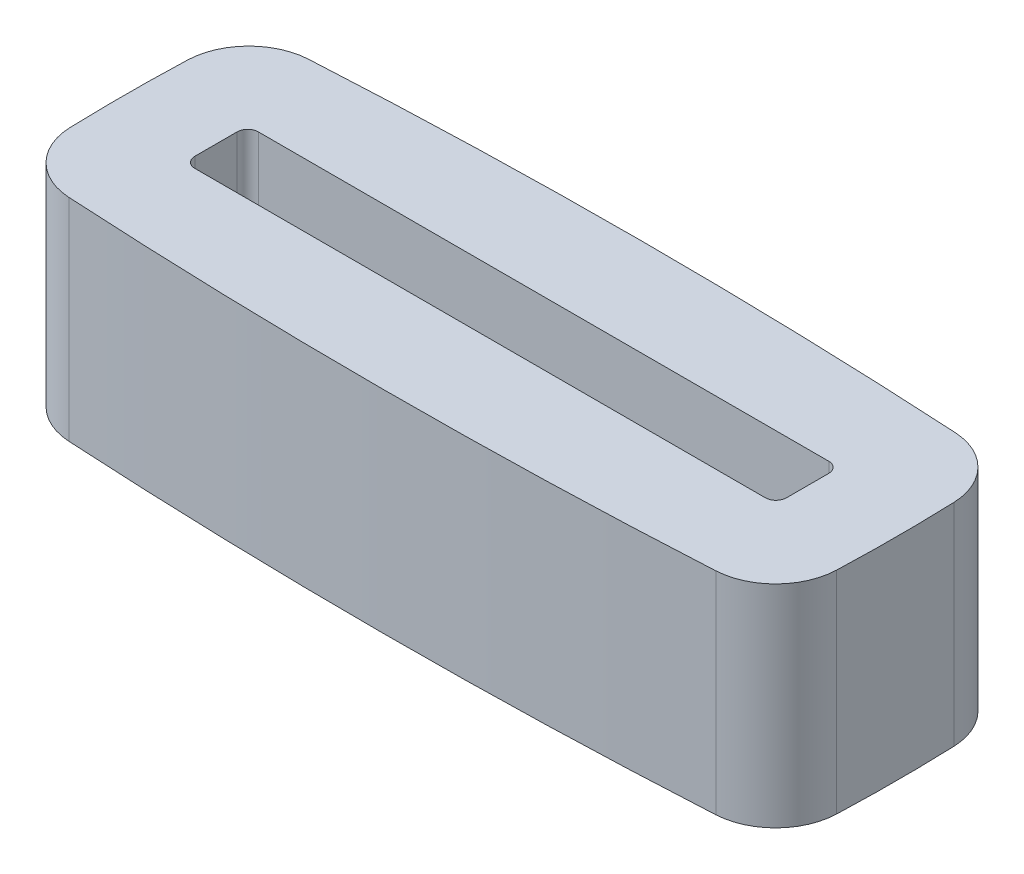
SolidWorks part; units mm, degrees
material "Медь"
ref_plane "Спереди" through (0, 0, 0) normal (0, 0, 1) x (1, 0, 0)
ref_plane "Сверху" through (0, 0, 0) normal (0, 1, 0) x (1, 0, 0)
ref_plane "Справа" through (0, 0, 0) normal (1, 0, 0) x (0, 0, -1)
sketch "Эскиз1" plane through (0, 0, 0) normal (0, 1, 0) x (1, 0, 0)
  line L7 (6.029, -0.585) -> (-21.971, -0.585)
  line L8 (6.029, -0.585) -> (6.029, 2.415)
  line L9 (6.029, 2.415) -> (-21.971, 2.415)
  line L10 (-21.971, -0.585) -> (-21.971, 2.415)
  arc A0 (-25.9419, 6.415) -> (10.029, 6.415) centre (-7.9565, -262.8497) cw
  arc A1 (-25.971, -4.585) -> (10.029, -4.585) centre (-7.971, 265.115) ccw
  arc A2 (-25.971, -4.585) -> (-25.9419, 6.415) centre (55.4935, 0.7001) cw
  arc A3 (10.029, 6.415) -> (10.029, -4.585) centre (-65.496, 0.915) cw
  point P1 (0, 0)
  point P6 (0, 0)
  point P15 (-7.9565, 7.015)
  point P16 (-7.971, -5.185)
  point P17 (-26.1419, 0.9155)
  point P18 (10.229, 0.915)
  dimension "D1" = 11
  dimension "D2" = 36
  dimension "D3" = 3
  dimension "D4" = 28
  dimension "D5" = 0.6
  dimension "D6" = 0.6
  dimension "D7" = 0.2
  dimension "D8" = 0.2
  dimension "D9" = 4
  dimension "D10" = 4
  dimension "D11" = 11
  dimension "D12" = 4
  dimension "D13" = 4
extrude "Бобышка-Вытянуть1" add sketch "Эскиз1" along normal blind 10
fillet "Скругление1" radius 3 4 edges at (-25.971, 5, 4.585) (10.029, 5, 4.585) (10.029, 5, -6.415) (-25.9419, 5, -6.415)
fillet "Скругление2" radius 0.5 4 edges at (-21.971, 5, 0.585) (-21.971, 5, -2.415) (6.029, 5, 0.585) (6.029, 5, -2.415)
